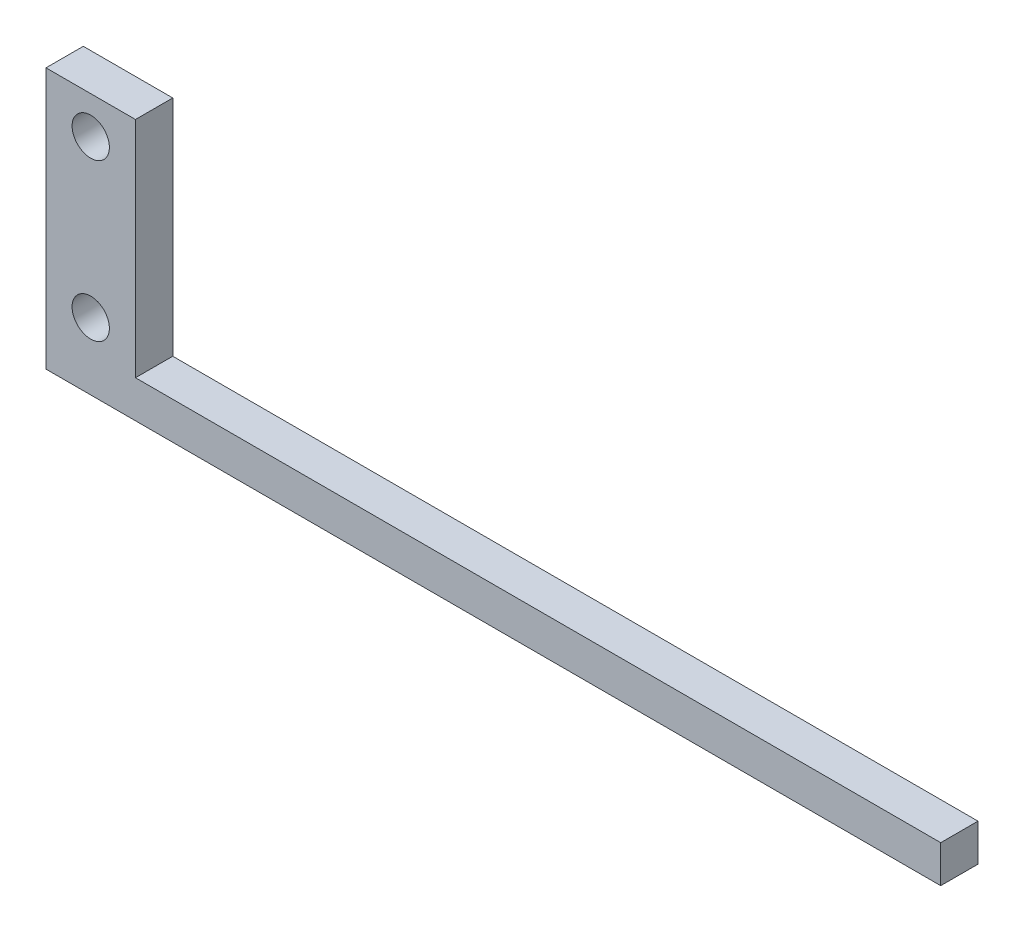
SolidWorks part; units mm, degrees
ref_plane "Front Plane" through (0, 0, 0) normal (0, 0, 1) x (1, 0, 0)
ref_plane "Top Plane" through (0, 0, 0) normal (0, 1, 0) x (1, 0, 0)
ref_plane "Right Plane" through (0, 0, 0) normal (1, 0, 0) x (0, 0, -1)
sketch "Sketch1" plane through (0, 0, 0) normal (0, 0, 1) x (1, 0, 0)
  line L0 (0, 0) -> (0, 38.1)
  line L1 (0, 38.1) -> (-15.24, 38.1)
  line L2 (-15.24, 38.1) -> (-15.24, -6.35)
  line L3 (-15.24, -6.35) -> (137.16, -6.35)
  line L4 (137.16, -6.35) -> (137.16, 0)
  line L5 (137.16, 0) -> (0, 0)
  point P3 (-7.62, 31.75)
  point P8 (-7.62, 0)
  dimension "D1" = 15.24
  dimension "D2" = 44.45
  dimension "D3" = 6.35
  dimension "D4" = 152.4
  dimension "D5" = 6.35
  dimension "D6" = 7.62
  dimension "D7" = 31.75
extrude "Boss-Extrude1" add sketch "Sketch1" along normal blind 6.35
sketch "Sketch3" plane through (0, 0, 0) normal (0, 0, -1) x (-1, 0, 0)
  line L0 (15.24, 38.1) -> (15.24, -6.35) construction
  line L3 (0, 38.1) -> (15.24, 38.1) construction
  point P0 (7.62, 31.75)
  point P1 (7.62, 5.0607)
  dimension "D1" = 7.62
  dimension "D2" = 6.35
hole_wizard "1/4 (0.25) Diameter Hole1" positions "3DSketch2" profile "Sketch4" hole size "1/4" standard "ANSI Inch" end condition through all
sketch3d "3DSketch2"
  point P0 (-7.62, 31.75, 0)
  point P3 (-7.62, 5.0607, 0)
sketch "Sketch4" plane through (-7.62, 31.75, 0) normal (1, 0, 0) x (0, 1, 0)
  line L0 (0, 0) -> (0, 6.35)
  line L1 (0, 6.35) -> (3.175, 6.35)
  line L2 (3.175, 6.35) -> (3.175, 0)
  line L5 (3.175, 0) -> (0, 0)
  line L11 (0, -6.35) -> (0, 107.95) construction
  dimension "Thru Hole Dia." = 6.35
  dimension "Thru Hole Depth" = 6.35
